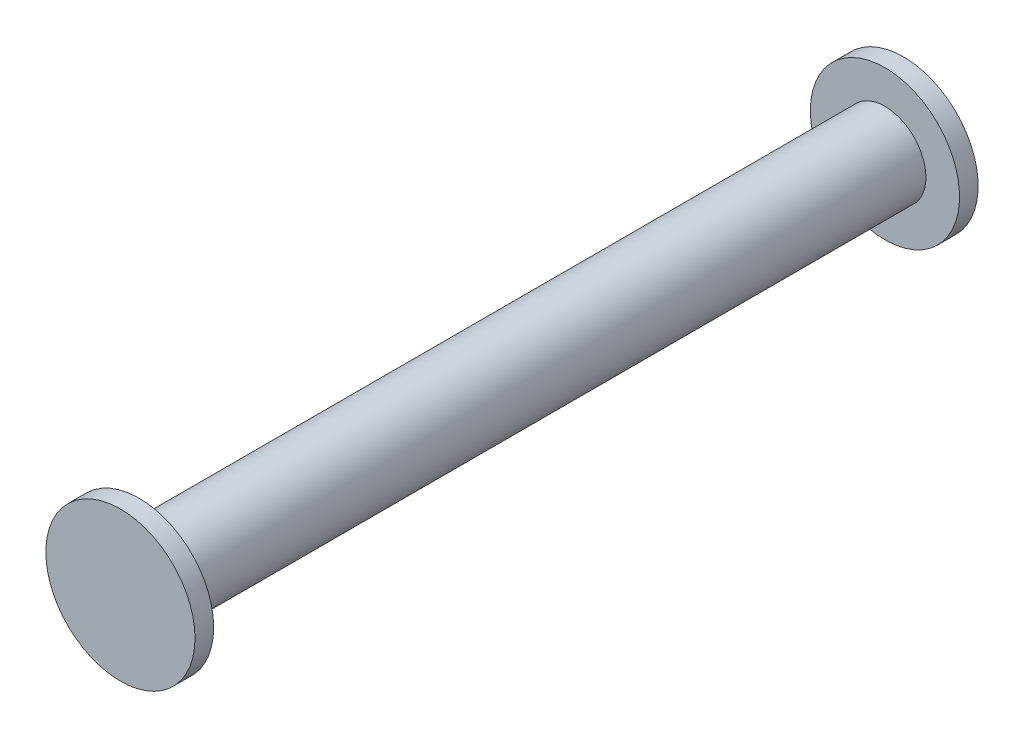
SolidWorks part; units mm, degrees
ref_plane "Front Plane" through (0, 0, 0) normal (0, 0, 1) x (1, 0, 0)
ref_plane "Top Plane" through (0, 0, 0) normal (0, 1, 0) x (1, 0, 0)
ref_plane "Right Plane" through (0, 0, 0) normal (1, 0, 0) x (0, 0, -1)
sketch "Sketch1" plane through (0, 0, 0) normal (0, 0, 1) x (1, 0, 0)
  circle A0 centre (-44.1117, 4.8883) radius 2.2
extrude "Boss-Extrude1" add sketch "Sketch1" against normal blind 40
sketch "Sketch2" plane through (0, 0, 0) normal (0, 0, 1) x (1, 0, 0)
  circle A0 centre (-44.1117, 4.8883) radius 4
extrude "Boss-Extrude2" add sketch "Sketch2" along normal blind 1
sketch "Sketch3" plane through (0, 0, -40) normal (0, 0, -1) x (-1, 0, 0)
  circle A0 centre (44.1117, 4.8883) radius 4
extrude "Boss-Extrude3" add sketch "Sketch3" along normal blind 1
